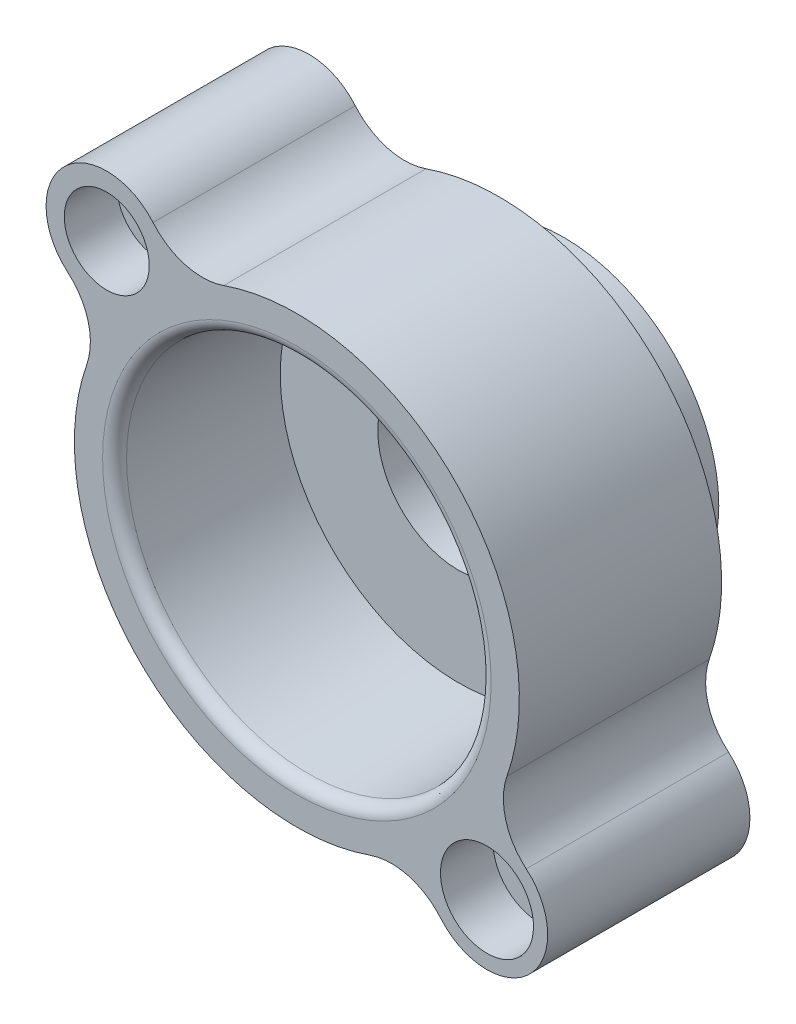
SolidWorks part; units mm, degrees
ref_plane "FRONT" through (0, 0, 0) normal (0, 0, 1) x (1, 0, 0)
ref_plane "TOP" through (0, 0, 0) normal (0, 1, 0) x (1, 0, 0)
ref_plane "RIGHT" through (0, 0, 0) normal (1, 0, 0) x (0, 0, -1)
ref_plane "Plan1" through (0, 0, 838.2) normal (0, 0, 1) x (1, 0, 0)
sketch "Esquisse1" plane through (0, 0, 838.2) normal (0, 0, 1) x (1, 0, 0)
  arc A0 (-229.7738, 659.6259) -> (-451.6018, 720.1018) centre (-296.617, 851.517) cw
  arc A1 (-451.6018, 720.1018) -> (-720.1018, 451.6018) centre (-596.9, 596.9) ccw
  arc A2 (-720.1018, 451.6018) -> (-659.6259, 229.7738) centre (-851.517, 296.617) cw
  arc A3 (-659.6259, 229.7738) -> (229.7738, -659.6259) centre (0, 0) ccw
  arc A4 (229.7738, -659.6259) -> (451.6018, -720.1018) centre (296.617, -851.517) cw
  arc A5 (451.6018, -720.1018) -> (720.1018, -451.6018) centre (596.9, -596.9) ccw
  arc A6 (720.1018, -451.6018) -> (659.6259, -229.7738) centre (851.517, -296.617) cw
  arc A7 (659.6259, -229.7738) -> (-229.7738, 659.6259) centre (0, 0) ccw
extrude "Boss.-Extru.1" add sketch "Esquisse1" against normal blind 635
sketch "Esquisse2" plane through (0, 0, 203.2) normal (0, 0, -1) x (-1, 0, 0)
  circle A0 centre (0, 0) radius 486.41
extrude "Boss.-Extru.2" add sketch "Esquisse2" along normal blind 203.2
sketch "Esquisse3" plane through (0, 0, 838.2) normal (0, 0, 1) x (1, 0, 0)
  circle A0 centre (0, 0) radius 572.77
extrude "Enlèv. mat.-Extru.1" cut sketch "Esquisse3" against normal blind 508 draft 1.432
sketch "Esquisse4" plane through (0, 0, 330.2) normal (0, 0, 1) x (1, 0, 0)
  circle A0 centre (0, 0) radius 254
extrude "Enlèv. mat.-Extru.2" cut sketch "Esquisse4" against normal through all
hole_wizard "Perçage1" positions "Esquisse6" profile "Esquisse5" legacy
sketch "Esquisse6" plane through (0, 0, 838.2) normal (0, 0, 1) x (1, 0, 0)
  point P0 (596.9, -596.9)
sketch "Esquisse5" plane through (596.9, -596.9, 838.2) normal (1, 0, 0) x (0, -1, 0)
  line L0 (0, 0) -> (0, 838.2)
  line L1 (0, 838.2) -> (69.85, 838.2)
  line L2 (69.85, 838.2) -> (69.85, 165.1)
  line L3 (69.85, 165.1) -> (146.05, 165.1)
  line L4 (146.05, 165.1) -> (146.05, 0)
  line L5 (146.05, 0) -> (0, 0)
  line L6 (0, 110) -> (0, -10) construction
  dimension "Diamètre" = 139.7
  dimension "Profondeur" = 838.2
  dimension "Diamètre chambrage" = 292.1
  dimension "Profondeur chambrage" = 165.1
hole_wizard "Perçage2" positions "Esquisse8" profile "Esquisse7" legacy
sketch "Esquisse8" plane through (0, 0, 838.2) normal (0, 0, 1) x (1, 0, 0)
  point P0 (-596.9, 596.9)
sketch "Esquisse7" plane through (-596.9, 596.9, 838.2) normal (1, 0, 0) x (0, -1, 0)
  line L0 (0, 0) -> (0, 838.2)
  line L1 (0, 838.2) -> (69.85, 838.2)
  line L2 (69.85, 838.2) -> (69.85, 165.1)
  line L3 (69.85, 165.1) -> (133.35, 165.1)
  line L4 (133.35, 165.1) -> (133.35, 0)
  line L5 (133.35, 0) -> (0, 0)
  line L6 (0, 110) -> (0, -10) construction
  dimension "Diamètre" = 139.7
  dimension "Profondeur" = 838.2
  dimension "Diamètre chambrage" = 266.7
  dimension "Profondeur chambrage" = 165.1
fillet "Congé1" radius 38.1 1 edges at (-572.77, 0, 838.2)
